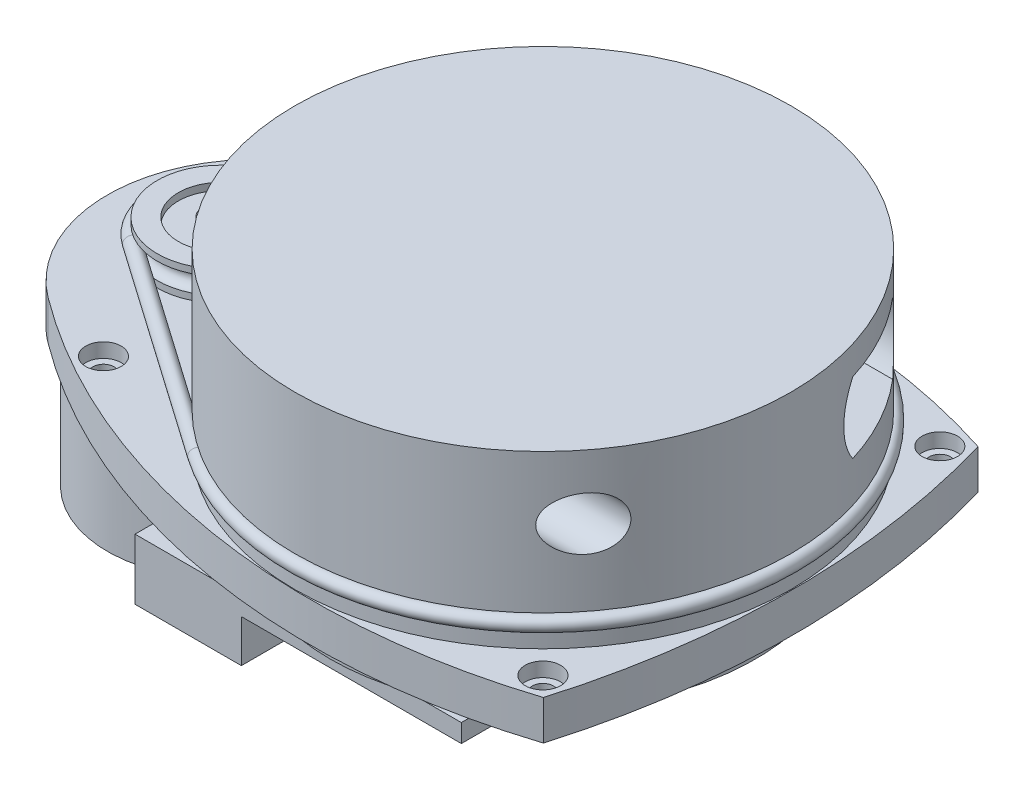
SolidWorks part; units mm, degrees
ref_plane "Front Plane" through (0, 0, 0) normal (0, 0, 1) x (1, 0, 0)
ref_plane "Top Plane" through (0, 0, 0) normal (0, 1, 0) x (1, 0, 0)
ref_plane "Right Plane" through (0, 0, 0) normal (1, 0, 0) x (0, 0, -1)
sketch "Sketch1" plane through (0, 0, 0) normal (0, 1, 0) x (1, 0, 0)
  line L0 (28, 28) -> (28, -28) construction
  line L1 (-55, 0) -> (55, 0) construction
  line L2 (-42, 20) -> (-42, -20) construction
  line L3 (-42.745, 21.3019) -> (-41.1392, 22.2207) construction
  line L4 (-42, 0) -> (28, 0) construction
  line L5 (-42.745, 21.3019) -> (-43.6638, 22.9076) construction
  line L6 (29.446, -28.3988) -> (30.1706, -25.7712) construction
  line L7 (30.1706, -25.7712) -> (29.446, -28.3988) construction
  line L8 (29.446, -28.3988) -> (31.2295, -28.8906) construction
  line L9 (28.432, -29.4364) -> (27.9895, -29.5695) construction
  line L10 (27.9895, -29.5695) -> (28.432, -29.4364) construction
  line L11 (28.432, -29.4364) -> (28.9648, -31.2081) construction
  line L12 (28.9648, -31.2081) -> (31.5329, -30.4357) construction
  line L13 (31.2295, -28.8906) -> (32.0862, -25.7839) construction
  circle A0 centre (28, -28) radius 1.5
  circle A1 centre (-42, -20) radius 1.5
  circle A2 centre (-42, 20) radius 1.5
  circle A3 centre (28, 28) radius 1.5
  arc A4 (-53.0254, 16.7712) -> (-53.0254, -16.7712) centre (-40.5194, 0) ccw
  arc A5 (30.7255, 30.6593) -> (30.7255, -30.6593) centre (-73.5351, 0) cw
  arc A6 (-53.0254, 16.7712) -> (30.7255, 30.6593) centre (2.3065, -57.4321) cw
  arc A7 (-53.0254, -16.7712) -> (30.7255, -30.6593) centre (2.3065, 57.4321) ccw
  circle A8 centre (-45.44, 0) radius 16 construction
  point P3 (28, 0)
  point P6 (-42, 0)
  point P20 (-61.44, 0)
  point P23 (35.14, 0)
  point P25 (2.3065, 35.13)
  point P26 (2.3065, -35.13)
  dimension "D5" = 3
  dimension "D12" = 32
  dimension "D1" = 42
  dimension "D2" = 28
  dimension "D3" = 56
  dimension "D4" = 40
  dimension "D6" = 40.5194
  dimension "D7" = 96.58
  dimension "D8" = 70.26
  dimension "D9" = 35.14
  dimension "D10" = 1.85
  dimension "D11" = 1.85
  dimension "D13" = 45.44
extrude "Boss-Extrude1" add sketch "Sketch1" along normal blind 5.57
sketch "Sketch17" plane through (0, 5.57, 0) normal (0, 1, 0) x (1, 0, 0)
  circle A0 centre (-42, 20) radius 2.5
  circle A1 centre (28, 28) radius 2.5
  circle A2 centre (28, -28) radius 2.5
  circle A3 centre (-42, -20) radius 2.5
  dimension "D1" = 5
extrude "Cut-Extrude3" cut sketch "Sketch17" against normal blind 2.03
sketch "Sketch3" plane through (0, 0, 0) normal (0, -1, 0) x (-1, 0, 0)
  circle A0 centre (0, 0) radius 30
  dimension "D1" = 60
extrude "Boss-Extrude2" add sketch "Sketch3" along normal blind 5.43
sketch "Sketch6" plane through (0, -5.43, 0) normal (0, -1, 0) x (-1, 0, 0)
  line L0 (-3.0635, 0) -> (3.0635, 0) construction
  line L1 (29.04, -28.505) -> (-17, -28.505)
  line L2 (29.04, -28.505) -> (29.04, 28.505)
  line L3 (29.04, 28.505) -> (-17, 28.505)
  line L4 (-17, -28.505) -> (-17, 28.505)
  line L5 (29.04, -28.505) -> (-17, 28.505) construction
  line L6 (29.04, 28.505) -> (-17, -28.505) construction
  circle A0 centre (0, 0) radius 30 construction
  circle A1 centre (0, 0) radius 30 construction
  point P0 (6.02, 0)
  point P7 (-30, 0)
  dimension "D1" = 46.04
  dimension "D2" = 57.01
  dimension "D3" = 13
ref_plane "Plane1" through (0, -8, 0) normal (0, -1, 0) x (-1, 0, 0)
extrude "Boss-Extrude3" add sketch "Sketch6" along normal up to surface (2.57 mm away) up to plane "Plane1"
ref_plane "Plane2" through (0, -14, 0) normal (0, -1, 0) x (-1, 0, 0)
sketch "Sketch7" plane through (0, -8, 0) normal (0, -1, 0) x (1, 0, 0)
  line L0 (3.0635, 0) -> (-3.0635, 0) construction
  line L1 (-14.04, -28.505) -> (-29.04, -28.505)
  line L2 (-14.04, -28.505) -> (-14.04, 28.505)
  line L3 (-14.04, 28.505) -> (-29.04, 28.505)
  line L4 (-29.04, -28.505) -> (-29.04, 28.505)
  line L5 (-14.04, -28.505) -> (-29.04, 28.505) construction
  line L6 (-14.04, 28.505) -> (-29.04, -28.505) construction
  line L7 (17, 28.505) -> (-29.04, 28.505) construction
  line L8 (-29.04, 28.505) -> (-29.04, -28.505) construction
  point P0 (-21.54, 0)
  dimension "D1" = 15
extrude "Boss-Extrude4" add sketch "Sketch7" along normal up to surface (6 mm away) up to plane "Plane2"
sketch "Sketch8" plane through (0, 0, 0) normal (0, -1, 0) x (1, 0, 0)
  arc A0 (-29.04, 7.5285) -> (-29.04, -7.5285) centre (0, 0) ccw construction
  arc A1 (-29.5691, 5.0665) -> (-29.5691, -5.0665) centre (0, 0) ccw
  circle A4 centre (-45.44, 0) radius 16.66
  arc A5 (-29.5691, -5.0665) -> (-29.5691, 5.0665) centre (-45.44, 0) ccw
  dimension "D1" = 0.66
extrude "Cut-Extrude1" cut sketch "Sketch8" along normal up to surface (5.43 mm away) up to face at (-29.52, -5.43, 0)
sketch "Sketch9" plane through (0, 0, 0) normal (0, -1, 0) x (1, 0, 0)
  circle A0 centre (-45.44, 0) radius 16 construction
  circle A1 centre (-45.44, 0) radius 16
extrude "Boss-Extrude5" add sketch "Sketch9" along normal blind 22
sketch "Sketch10" plane through (0, 5.57, 0) normal (0, 1, 0) x (1, 0, 0)
  circle A0 centre (-45.44, 0) radius 0.42
  dimension "D1" = 0.84
extrude "Boss-Extrude6" add sketch "Sketch10" along normal blind 2.9
sketch "Sketch13" plane through (0, 0, 0) normal (0, 0, 1) x (1, 0, 0)
  line L0 (-45.44, 5.57) -> (-45.44, 11.7334) construction
  line L1 (-45.44, 8.47) -> (-45.44, 5.57) construction
  line L2 (30.7255, 5.57) -> (-53.0254, 5.57) construction
  line L3 (-45.02, 5.57) -> (-45.02, 10.86)
  line L4 (-45.02, 10.86) -> (-42.94, 10.86)
  line L5 (-42.94, 10.86) -> (-42.94, 9.84)
  line L6 (-42.94, 9.84) -> (-39.45, 9.84)
  line L7 (-39.45, 9.84) -> (-39.45, 10.86)
  line L8 (-39.45, 10.86) -> (-36.47, 10.86)
  line L9 (-36.47, 10.86) -> (-36.47, 9.95)
  line L10 (-36.47, 7.58) -> (-36.47, 6.67)
  line L11 (-36.47, 6.67) -> (-39.45, 6.67)
  line L12 (-39.45, 6.67) -> (-39.45, 7.69)
  line L13 (-39.45, 7.69) -> (-42.94, 7.69)
  line L14 (-42.94, 7.69) -> (-42.94, 5.57)
  line L15 (-42.94, 5.57) -> (-45.02, 5.57)
  arc A0 (-36.47, 9.95) -> (-36.47, 7.58) centre (-36.47, 8.765) ccw
  dimension "D1" = 0.91
  dimension "D2" = 2.37
  dimension "D3" = 5.29
  dimension "D4" = 1.02
  dimension "D5" = 2.98
  dimension "D6" = 17.94
  dimension "D7" = 5
revolve "Revolve1" add sketch "Sketch13" angle 360 about L0
sketch "Sketch14" plane through (0, 5.57, 0) normal (0, 1, 0) x (1, 0, 0)
  circle A0 centre (0, 0) radius 2.5
  dimension "D1" = 5
extrude "Cut-Extrude2" cut sketch "Sketch14" against normal up to surface (5.57 mm away) up to face at (0.61, 0, 0)
sketch "Sketch16" plane through (0, 0, 0) normal (0, 0, 1) x (1, 0, 0)
  line L0 (0, 5.57) -> (0, 29.68) construction
  line L1 (0, -18.073) -> (0, 18.073) construction
  line L2 (30.7255, 5.57) -> (-53.0254, 5.57) construction
  line L3 (0, 29.68) -> (0, 10.57)
  line L4 (-2.5, 5.57) -> (-35, 5.57)
  line L5 (-35, 5.57) -> (-35, 7.58)
  line L6 (-35, 9.95) -> (-35, 29.68)
  line L7 (-35, 29.68) -> (0, 29.68)
  line L8 (-2.5, 5.57) -> (-2.5, 10.57)
  line L9 (-2.5, 10.57) -> (0, 10.57)
  line L10 (-35, 8.765) -> (-2.5, 8.765) construction
  arc A0 (-35, 7.58) -> (-35, 9.95) centre (-35, 8.765) ccw
  arc A1 (-36.47, 9.95) -> (-36.47, 7.58) centre (-36.47, 8.765) ccw construction
  dimension "D1" = 5
  dimension "D2" = 70
  dimension "D3" = 24.11
  dimension "D4" = 5
revolve "Revolve2" add sketch "Sketch16" angle 360 about L0
ref_plane "Plane3" through (35, 0, 0) normal (1, 0, 0) x (0, 0, -1)
sketch "Sketch18" plane through (35, 0, 0) normal (1, 0, 0) x (0, 0, -1)
  line L0 (-23.8858, 25.68) -> (22.745, 25.68) construction
  line L2 (-23.9642, 15.68) -> (22.745, 15.68) construction
  line L5 (22.745, 25.68) -> (22.745, 15.68) construction
  line L6 (35, 29.68) -> (-35, 29.68) construction
  line L7 (22.745, 20.68) -> (-23.8858, 20.68) construction
  line L8 (22.745, 25.68) -> (10.255, 25.68)
  line L9 (22.745, 15.68) -> (10.255, 15.68)
  line L10 (0, 28.424) -> (0, -28.424) construction
  arc A0 (10.255, 25.68) -> (10.255, 15.68) centre (16.5, 20.68) ccw
  circle A1 centre (-21.5, 20.68) radius 3.75
  arc A2 (22.745, 25.68) -> (10.255, 25.68) centre (16.5, 20.68) ccw construction
  arc A3 (10.255, 15.68) -> (22.745, 15.68) centre (16.5, 20.68) ccw construction
  arc A4 (22.745, 15.68) -> (22.745, 25.68) centre (16.5, 20.68) ccw
  point P0 (22.745, 20.68)
  point P3 (-0.5704, 25.68)
  point P6 (-0.6096, 15.68)
  point P15 (9.2476, 15.68)
  dimension "D3" = 7.5
  dimension "D4" = 16
  dimension "D1" = 10
  dimension "D2" = 9
  dimension "D5" = 38
  dimension "D6" = 16.5
extrude "Cut-Extrude4" cut sketch "Sketch18" against normal blind 24
ref_plane "Plane4" through (0, 8.765, 0) normal (0, 1, 0) x (1, 0, 0)
sketch "Sketch19" plane through (0, 8.765, 0) normal (0, 1, 0) x (1, 0, 0)
  line L0 (-50.5784, 7.3524) -> (-20.0495, 28.6883)
  line L1 (-50.5784, -7.3524) -> (-20.0495, -28.6883)
  circle A0 centre (-45.44, 0) radius 8.97 construction
  circle A1 centre (0, 0) radius 35
  arc A2 (-20.0495, -28.6883) -> (-20.0495, 28.6883) centre (0, 0) ccw
  arc A3 (-50.5784, 7.3524) -> (-50.5784, -7.3524) centre (-45.44, 0) ccw
  arc A4 (-20.0495, 28.6883) -> (-20.0495, -28.6883) centre (0, 0) ccw construction
  arc A5 (-50.5784, -7.3524) -> (-50.5784, 7.3524) centre (-45.44, 0) ccw construction
  point P4 (-54.41, 0)
  dimension "D1" = 0
sketch "Sketch21" plane through (0, 0, 0) normal (0, 0, 1) x (1, 0, 0)
  circle A0 centre (-54.41, 8.765) radius 1
  dimension "D1" = 2
sweep "Sweep1" add profiles "Sketch21" path "Sketch19"
ref_plane "Plane5" through (0, 20.68, 0) normal (0, 1, 0) x (1, 0, 0)
sketch "Sketch22" plane through (0, 20.68, 0) normal (0, 1, 0) x (1, 0, 0)
  point P0 (0, 0)
  point P1 (3.6155, -3.7449)
